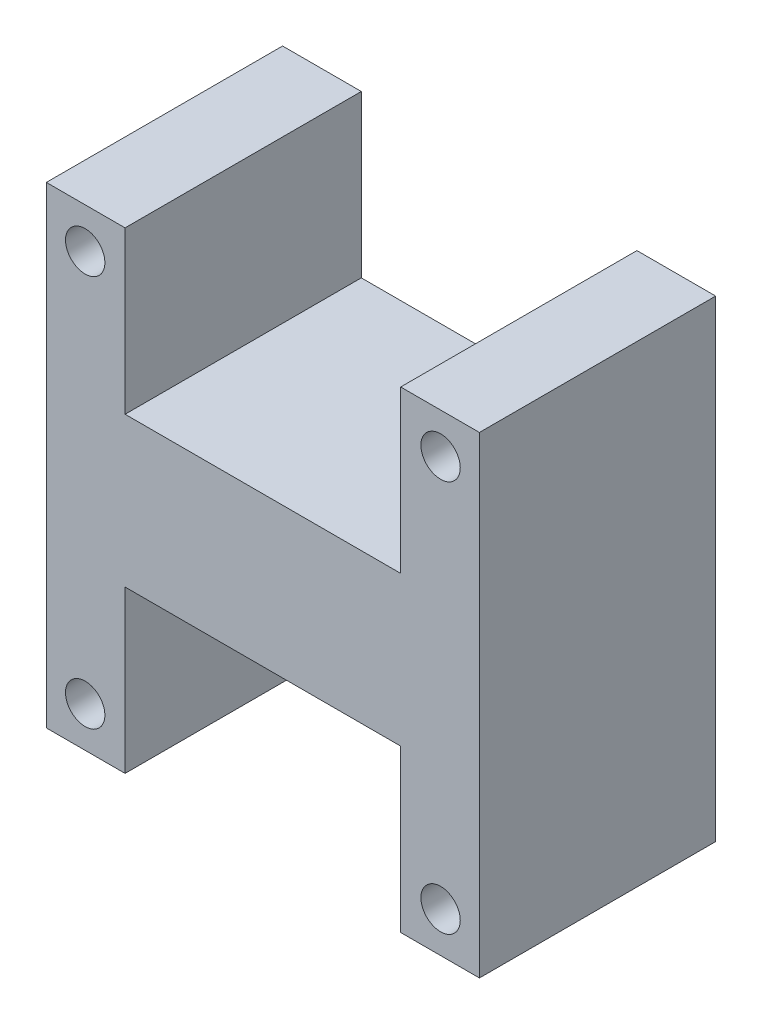
SolidWorks part; units mm, degrees
ref_plane "Front Plane" through (0, 0, 0) normal (0, 0, 1) x (1, 0, 0)
ref_plane "Top Plane" through (0, 0, 0) normal (0, 1, 0) x (1, 0, 0)
ref_plane "Right Plane" through (0, 0, 0) normal (1, 0, 0) x (0, 0, -1)
sketch "Sketch1" plane through (0, 0, 0) normal (0, 0, 1) x (1, 0, 0)
  line L0 (0, 38.1) -> (69.85, 38.1) construction
  line L1 (0, 0) -> (69.85, 0)
  line L2 (0, 0) -> (0, 76.2)
  line L3 (0, 76.2) -> (69.85, 76.2)
  line L4 (69.85, 0) -> (69.85, 76.2)
  line L5 (12.7, 76.2) -> (57.15, 76.2)
  line L6 (12.7, 76.2) -> (12.7, 50.165)
  line L7 (12.7, 50.165) -> (57.15, 50.165)
  line L8 (57.15, 76.2) -> (57.15, 50.165)
  line L9 (12.7, 26.035) -> (57.15, 26.035)
  line L10 (12.7, 0) -> (12.7, 26.035)
  line L11 (57.15, 0) -> (57.15, 26.035)
  line L12 (12.7, 0) -> (57.15, 0)
  line L13 (34.925, 76.2) -> (34.925, 0) construction
  line L14 (34.925, 0) -> (34.925, 76.2) construction
  circle A1 centre (6.2656, 6.4977) radius 3.175
  circle A2 centre (63.5844, 6.4977) radius 3.175
  circle A3 centre (6.2656, 69.7023) radius 3.175
  circle A4 centre (63.5844, 69.7023) radius 3.175
  dimension "D5" = 6.35
  dimension "D6" = 24.13
  dimension "D1" = 69.85
  dimension "D2" = 44.45
  dimension "D3" = 12.7
  dimension "D4" = 76.2
extrude "Boss-Extrude2" add sketch "Sketch1" along normal blind 38.1 contours L11 L1 L4 L3 L8 L7 L6 L2 L10 L9 A4 A2 A1 A3
